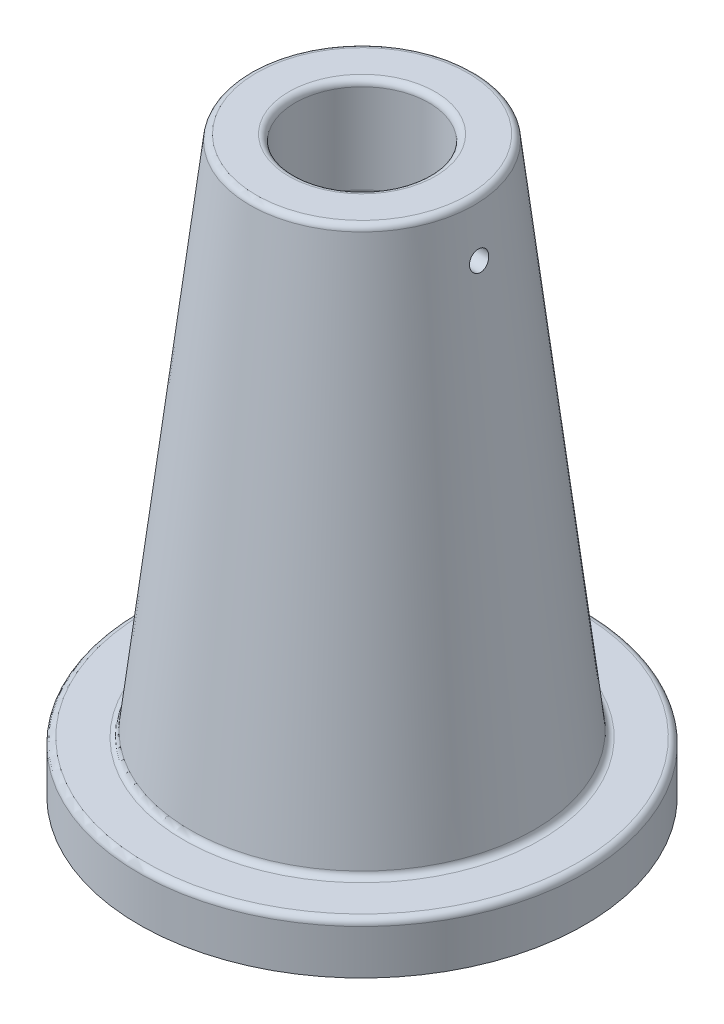
SolidWorks part; units mm, degrees
material "灰铸铁"
ref_plane "前视基准面" through (0, 0, 0) normal (0, 0, 1) x (1, 0, 0)
ref_plane "上视基准面" through (0, 0, 0) normal (0, 1, 0) x (1, 0, 0)
ref_plane "右视基准面" through (0, 0, 0) normal (1, 0, 0) x (0, 0, -1)
other "Configuration Table"
sketch "草图2" plane through (0, 0, 0) normal (0, 0, 1) x (1, 0, 0)
  line L0 (0, 180) -> (0, 148)
  line L1 (0, 148) -> (-29.6828, 148)
  line L2 (-29.6828, 148) -> (-47, 0)
  line L3 (-47, 0) -> (-70, 0)
  line L4 (-70, 0) -> (-70, 16)
  line L5 (-70, 16) -> (-54.1893, 16)
  line L6 (-54.1893, 16) -> (-35, 180)
  line L7 (-35, 180) -> (0, 180)
  dimension "D1" = 32
  dimension "D2" = 9
  dimension "D3" = 35
  dimension "D4" = 16
  dimension "D5" = 47
  dimension "D6" = 70
  dimension "D7" = 180
revolve "旋转1" add sketch "草图2" angle 360 about L0
sketch "草图3" plane through (0, 180, 0) normal (0, 1, 0) x (1, 0, 0)
  circle A0 centre (0, 0) radius 21
  dimension "D1" = 42
extrude "切除-拉伸1" cut sketch "草图3" against normal up to next
sketch "草图4" plane through (0, 0, 0) normal (1, 0, 0) x (0, 0, -1)
  line L0 (35, 180) -> (-35, 180) construction
  circle A0 centre (0, 164) radius 3
  dimension "D2" = 6
  dimension "D1" = 16
extrude "切除-拉伸2" cut sketch "草图4" along normal through all
fillet "圆角1" radius 2 6 edges at (21, 148, 0) (-21, 180, 0) (-29.6828, 148, 0) (-70, 16, 0) (-54.1893, 16, 0) (-35, 180, 0)
